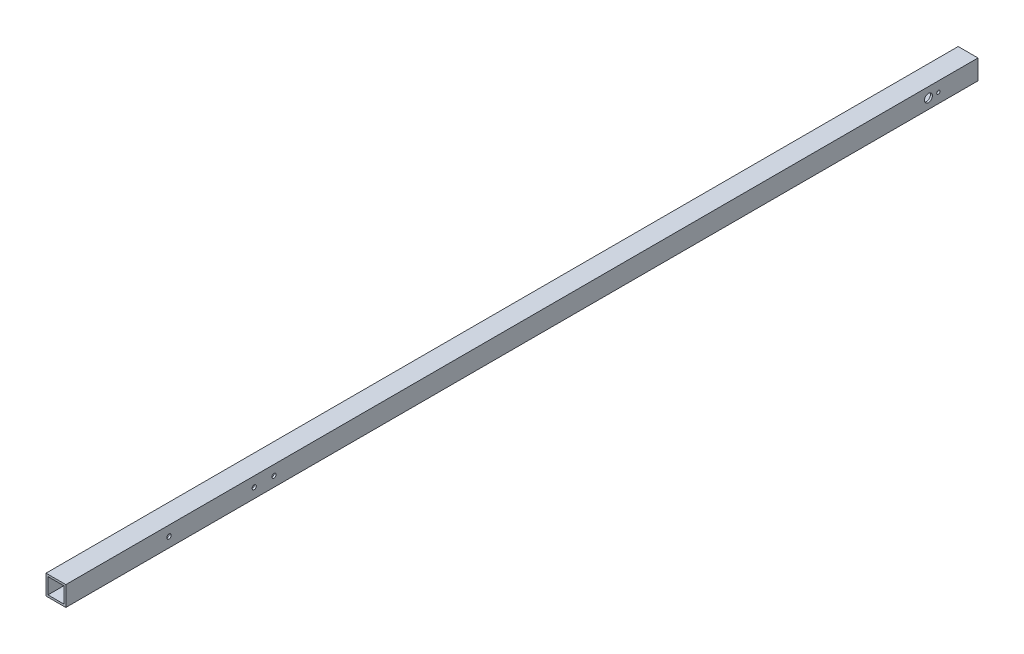
SolidWorks part; units mm, degrees
ref_plane "正面" through (0, 0, 0) normal (0, 0, 1) x (1, 0, 0)
ref_plane "平面" through (0, 0, 0) normal (0, 1, 0) x (1, 0, 0)
ref_plane "右側面" through (0, 0, 0) normal (1, 0, 0) x (0, 0, -1)
sketch "ｽｹｯﾁ1" plane through (0, 0, 0) normal (0, 0, 1) x (1, 0, 0)
  line L1 (-10, 10) -> (10, 10)
  line L2 (-10, 10) -> (-10, -10)
  line L3 (-10, -10) -> (10, -10)
  line L4 (10, 10) -> (10, -10)
  line L5 (-10, 10) -> (10, -10) construction
  line L6 (-10, -10) -> (10, 10) construction
  line L7 (-8, 8) -> (8, 8)
  line L8 (-8, 8) -> (-8, -8)
  line L9 (-8, -8) -> (8, -8)
  line L10 (8, 8) -> (8, -8)
  line L11 (-8, 8) -> (8, -8) construction
  line L12 (-8, -8) -> (8, 8) construction
  point P0 (0, 0)
  point P6 (0, 0)
  dimension "D1" = 20
  dimension "D2" = 20
  dimension "D3" = 16
  dimension "D4" = 16
extrude "ﾎﾞｽ - 押し出し1" add sketch "ｽｹｯﾁ1" along normal blind 970
sketch "ｽｹｯﾁ2" plane through (10, 0, 0) normal (1, 0, 0) x (0, 0, -1)
  line L0 (-970, 0) -> (-710, 0)
  line L1 (-970, -10) -> (-970, 10) construction
  line L2 (-710, 0) -> (-890.4665, 0)
  line L3 (-890.4665, 0) -> (-845.8821, 0)
  line L4 (-845.8821, 0) -> (-803.5394, 0)
  line L5 (-710, 0) -> (-670, 0)
  line L6 (-670, 0) -> (-50, 0)
  line L7 (-50, 0) -> (-40, 0)
  line L8 (-670, 0) -> (-650, 0)
  line L9 (-710, 0) -> (-730, 0)
  circle A0 centre (-710, 0) radius 1
  circle A4 centre (-670, 0) radius 2.2
  circle A5 centre (-50, 0) radius 4.05
  circle A6 centre (-40, 0) radius 1
  circle A7 centre (-650, 0) radius 2.1
  circle A8 centre (-730, 0) radius 1
  dimension "D5" = 2
  dimension "D6" = 8.1
  dimension "D7" = 4.4
  dimension "D8" = 2
  dimension "D10" = 4.2
  dimension "D12" = 2
  dimension "D1" = 260
  dimension "D2" = 40
  dimension "D3" = 620
  dimension "D4" = 10
  dimension "D9" = 20
  dimension "D11" = 20
extrude "ｶｯﾄ - 押し出し1" cut sketch "ｽｹｯﾁ2" against normal blind 20 contours L6 A5 L7 | L7 A5 L6 | A0
sketch "ｽｹｯﾁ3" plane through (0, 10, 0) normal (0, 1, 0) x (1, 0, 0)
  line L0 (0, -970) -> (0, -690)
  line L1 (10, -970) -> (-10, -970) construction
  line L2 (0, -690) -> (0, -670)
  line L3 (0, -670) -> (0, -10)
  line L4 (0, -670) -> (0, -650)
  line L5 (0, -650) -> (0, -630)
  circle A0 centre (0, -690) radius 2.1
  circle A1 centre (0, -670) radius 1
  circle A2 centre (0, -10) radius 2.2
  circle A3 centre (0, -650) radius 1
  circle A4 centre (0, -630) radius 2.1
  dimension "D2" = 4.2
  dimension "D4" = 2
  dimension "D6" = 4.4
  dimension "D7" = 2
  dimension "D9" = 4.2
  dimension "D1" = 280
  dimension "D3" = 20
  dimension "D5" = 20
  dimension "D8" = 20
sketch "ｽｹｯﾁ4" plane through (0, 0, 970) normal (0, 0, 1) x (1, 0, 0)
  line L1 (10.6881, 14.5445) -> (-10.6881, 14.5445)
  line L2 (10.6881, 14.5445) -> (10.6881, -14.5445)
  line L3 (10.6881, -14.5445) -> (-10.6881, -14.5445)
  line L4 (-10.6881, 14.5445) -> (-10.6881, -14.5445)
  line L5 (10.6881, 14.5445) -> (-10.6881, -14.5445) construction
  line L6 (10.6881, -14.5445) -> (-10.6881, 14.5445) construction
  point P0 (0, 0)
extrude "ｶｯﾄ - 押し出し3" cut sketch "ｽｹｯﾁ4" against normal blind 50
sketch "ｽｹｯﾁ5" plane through (10, 0, 0) normal (1, 0, 0) x (0, 0, -1)
  line L0 (-710, 0) -> (-816, 0)
  circle A0 centre (-816, 0) radius 2.2
  dimension "D2" = 4.4
  dimension "D1" = 106
extrude "ｶｯﾄ - 押し出し4" cut sketch "ｽｹｯﾁ5" against normal blind 30
sketch "ｽｹｯﾁ6" plane through (0, -10, 0) normal (0, -1, 0) x (1, 0, 0)
  line L0 (0, 0) -> (0, 30)
  line L1 (0, 30) -> (0, 50)
  circle A0 centre (0, 30) radius 1
  circle A1 centre (0, 50) radius 1
  dimension "D3" = 2
  dimension "D4" = 2
  dimension "D1" = 30
  dimension "D2" = 20
extrude "ｶｯﾄ - 押し出し5" cut sketch "ｽｹｯﾁ6" against normal blind 10
hole_wizard "M4x0.7 ねじ穴1" positions "3Dｽｹｯﾁ1" profile "ｽｹｯﾁ7" tap size "M4x0.7" standard "JIS"
sketch3d "3Dｽｹｯﾁ1"
  line L0 (0, -8, 30) -> (0, -10, 30) construction
  line L1 (0, -8, 50) -> (0, -10, 50) construction
  point P0 (0, -10, 30)
  point P4 (0, -10, 50)
cosmetic thread "穴のねじ山1" parameters "D1"=2, "D2"=4
cosmetic thread "穴のねじ山2" parameters "D1"=2, "D2"=4
sketch "ｽｹｯﾁ7" plane through (0, -10, 30) normal (1, 0, 0) x (0, 0, -1)
  line L0 (0, 0) -> (0, 12.4914)
  line L1 (0, 12.4914) -> (1.65, 11.5)
  line L2 (1.65, 11.5) -> (1.65, 0)
  line L5 (1.65, 0) -> (0, 0)
  line L10 (0, 12.4914) -> (-1.65, 11.5) construction
  line L11 (0, -6.35) -> (0, 107.95) construction
  dimension "ねじ下穴ﾄﾞﾘﾙ直径" = 3.3
  dimension "ねじ下穴ﾄﾞﾘﾙの深さ" = 11.5
  dimension "ﾄﾞﾘﾙ角度" = 118
sketch "ｽｹｯﾁ10" plane through (-10, 0, 0) normal (-1, 0, 0) x (0, 0, 1)
  line L0 (0, 0) -> (40, 0)
  line L1 (0, 10) -> (0, -10) construction
  line L2 (920, 0) -> (730, 0)
  line L3 (920, -10) -> (920, 10) construction
  line L4 (730, 0) -> (710, 0)
  circle A0 centre (40, 0) radius 1
  circle A1 centre (730, 0) radius 1
  circle A2 centre (710, 0) radius 1
  dimension "D2" = 2
  dimension "D5" = 2
  dimension "D6" = 2
  dimension "D1" = 40
  dimension "D3" = 190
  dimension "D4" = 20
sketch "ｽｹｯﾁ12" plane through (10, 0, 0) normal (1, 0, 0) x (0, 0, -1)
  line L0 (0, 0) -> (-40, 0)
  line L1 (0, -10) -> (0, 10) construction
  line L2 (-920, 0) -> (-730, 0)
  line L3 (-920, 10) -> (-920, -10) construction
  line L4 (-730, 0) -> (-710, 0)
  circle A0 centre (-40, 0) radius 1
  circle A1 centre (-710, 0) radius 1
  circle A2 centre (-730, 0) radius 1
  dimension "D2" = 2
  dimension "D5" = 2
  dimension "D6" = 2
  dimension "D1" = 40
  dimension "D3" = 190
  dimension "D4" = 20
extrude "ｶｯﾄ - 押し出し7" cut sketch "ｽｹｯﾁ12" against normal blind 10
hole_wizard "M4x0.7 ねじ穴6" positions "3Dｽｹｯﾁ6" profile "ｽｹｯﾁ14" tap size "M4x0.7" standard "JIS"
sketch3d "3Dｽｹｯﾁ6"
  line L0 (8, 0, 40) -> (10, 0, 40) construction
  point P0 (10, 0, 40)
sketch "ｽｹｯﾁ14" plane through (10, 0, 40) normal (0, 1, 0) x (0, 0, -1)
  line L0 (0, 0) -> (0, 12.4914)
  line L1 (0, 12.4914) -> (1.65, 11.5)
  line L2 (1.65, 11.5) -> (1.65, 0)
  line L5 (1.65, 0) -> (0, 0)
  line L10 (0, 12.4914) -> (-1.65, 11.5) construction
  line L11 (0, -6.35) -> (0, 107.95) construction
  dimension "ねじ下穴ﾄﾞﾘﾙ直径" = 3.3
  dimension "ねじ下穴ﾄﾞﾘﾙの深さ" = 11.5
  dimension "ﾄﾞﾘﾙ角度" = 118
cosmetic thread "穴のねじ山14" parameters "D1"=2, "D2"=4
sketch "ｽｹｯﾁ15" plane through (10, 0, 0) normal (1, 0, 0) x (0, 0, -1)
  circle A0 centre (-710, 0) radius 2.1
  circle A1 centre (-730, 0) radius 2.1
  dimension "D1" = 4.2
  dimension "D2" = 4.2
extrude "ｶｯﾄ - 押し出し8" cut sketch "ｽｹｯﾁ15" against normal through all
sketch "ｽｹｯﾁ16" plane through (0, -10, 0) normal (0, -1, 0) x (-1, 0, 0)
  line L0 (0, -920) -> (0, -670)
  line L1 (-10, -920) -> (10, -920) construction
  line L2 (0, -670) -> (0, -650)
  circle A0 centre (0, -670) radius 1
  circle A1 centre (0, -650) radius 1
  dimension "D3" = 2
  dimension "D4" = 2
  dimension "D1" = 250
  dimension "D2" = 20
extrude "ｶｯﾄ - 押し出し9" cut sketch "ｽｹｯﾁ16" against normal blind 10
hole_wizard "M4x0.7 ねじ穴7" positions "3Dｽｹｯﾁ7" profile "ｽｹｯﾁ17" tap size "M4x0.7" standard "JIS"
sketch3d "3Dｽｹｯﾁ7"
  line L0 (0, -8, 670) -> (0, -10, 670) construction
  line L1 (0, -8, 650) -> (0, -10, 650) construction
  point P0 (0, -10, 670)
  point P4 (0, -10, 650)
sketch "ｽｹｯﾁ17" plane through (0, -10, 670) normal (1, 0, 0) x (0, 0, -1)
  line L0 (0, 0) -> (0, 12.4914)
  line L1 (0, 12.4914) -> (1.65, 11.5)
  line L2 (1.65, 11.5) -> (1.65, 0)
  line L5 (1.65, 0) -> (0, 0)
  line L10 (0, 12.4914) -> (-1.65, 11.5) construction
  line L11 (0, -6.35) -> (0, 107.95) construction
  dimension "ねじ下穴ﾄﾞﾘﾙ直径" = 3.3
  dimension "ねじ下穴ﾄﾞﾘﾙの深さ" = 11.5
  dimension "ﾄﾞﾘﾙ角度" = 118
cosmetic thread "穴のねじ山15" parameters "D1"=2, "D2"=4
cosmetic thread "穴のねじ山16" parameters "D1"=2, "D2"=4
